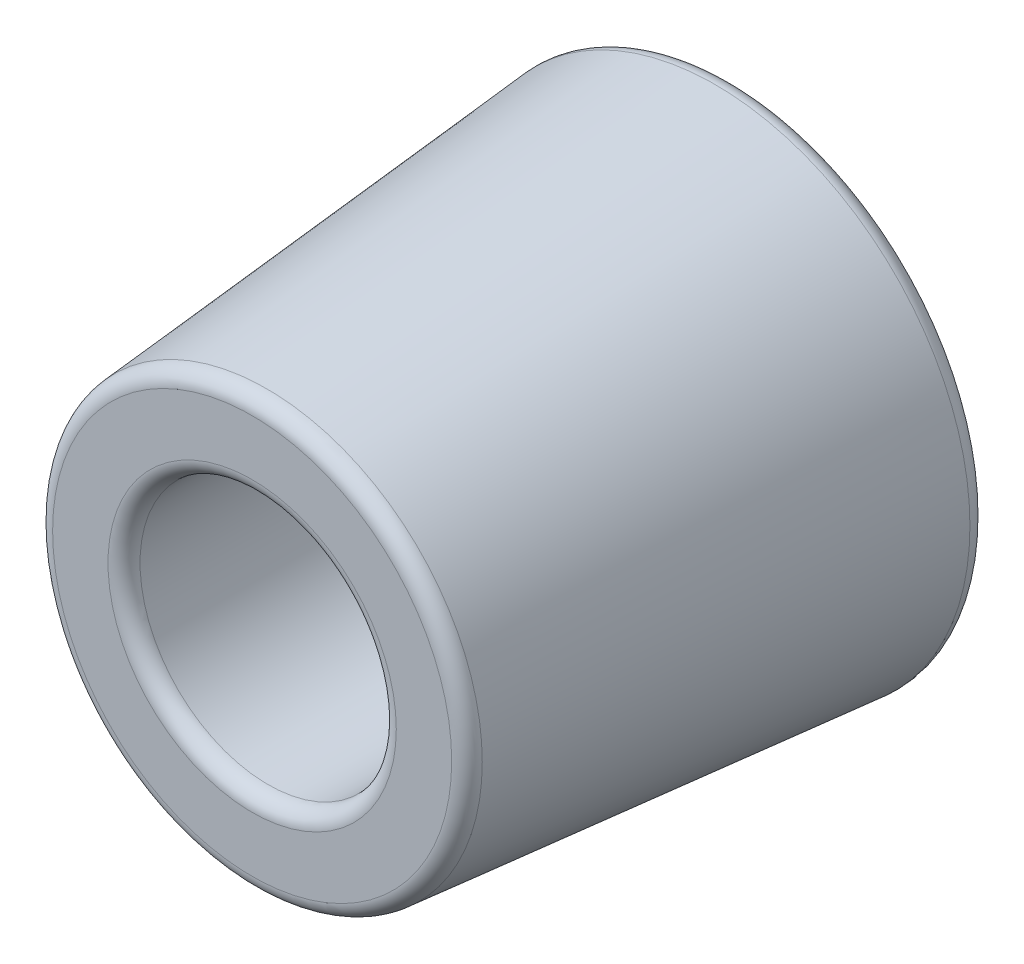
SolidWorks part; units mm, degrees
material "Caoutchouc silicone"
ref_plane "Plan de face" through (0, 0, 0) normal (0, 0, 1) x (1, 0, 0)
ref_plane "Plan de dessus" through (0, 0, 0) normal (0, 1, 0) x (1, 0, 0)
ref_plane "Plan de droite" through (0, 0, 0) normal (1, 0, 0) x (0, 0, -1)
sketch "Esquisse1" plane through (0, 0, 0) normal (0, 0, 1) x (1, 0, 0)
  circle A0 centre (0, 0) radius 8
  dimension "D1" = 16
extrude "Boss.-Extru.1" add sketch "Esquisse1" along normal blind 15 draft 5
sketch "Esquisse2" plane through (0, 0, 15) normal (0, 0, 1) x (1, 0, 0)
  circle A0 centre (0, 0) radius 2.5
extrude "Enlèv. mat.-Extru.1" cut sketch "Esquisse2" against normal blind 30
sketch "Esquisse3" plane through (0, 0, 15) normal (0, 0, 1) x (1, 0, 0)
  circle A0 centre (0, 0) radius 4
  dimension "D1" = 8
extrude "Enlèv. mat.-Extru.2" cut sketch "Esquisse3" against normal blind 10
fillet "Congé2" radius 0.5 1 edges at (4, 0, 15)
fillet "Congé3" radius 0.5 1 edges at (8, 0, 0)
fillet "Congé4" radius 0.5 1 edges at (6.6877, 0, 15)
